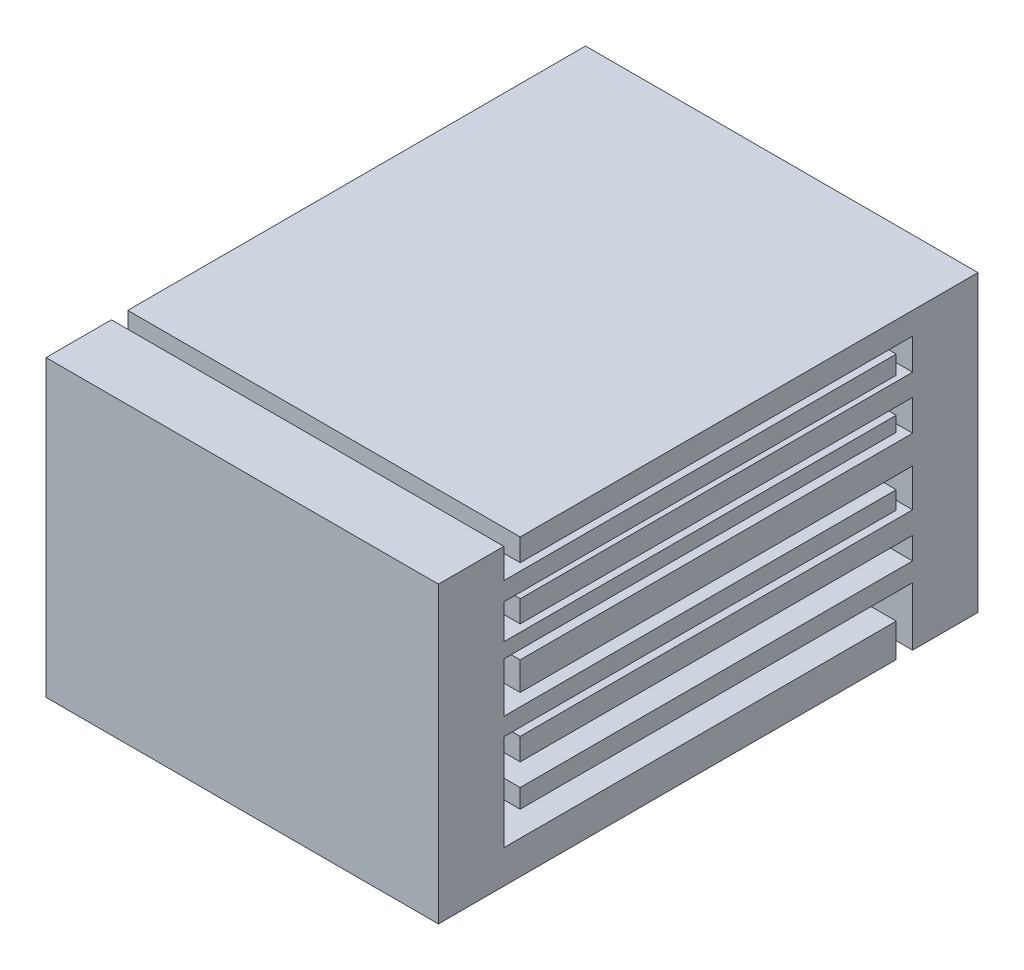
SolidWorks part; units mm, degrees
ref_plane "Front Plane" through (0, 0, 0) normal (0, 0, 1) x (1, 0, 0)
ref_plane "Top Plane" through (0, 0, 0) normal (0, 1, 0) x (1, 0, 0)
ref_plane "Right Plane" through (0, 0, 0) normal (1, 0, 0) x (0, 0, -1)
sketch "Sketch1" plane through (0, 0, 0) normal (0, 0, 1) x (1, 0, 0)
  line L1 (-60, 45) -> (60, 45)
  line L2 (-60, 45) -> (-60, -45)
  line L3 (-60, -45) -> (60, -45)
  line L4 (60, 45) -> (60, -45)
  line L5 (-60, 45) -> (60, -45) construction
  line L6 (-60, -45) -> (60, 45) construction
  point P0 (0, 0)
  dimension "D1" = 90
  dimension "D2" = 120
extrude "Boss-Extrude1" add sketch "Sketch1" along normal blind 20
sketch "Sketch2" plane through (0, 0, 20) normal (0, 0, 1) x (1, 0, 0)
  line L0 (60, -45) -> (60, 45) construction
  line L1 (-60, 45) -> (60, 45)
  line L2 (-60, 45) -> (-60, 38.1749)
  line L3 (-60, 38.1749) -> (60, 38.1749)
  line L4 (60, 45) -> (60, 38.1749)
  line L5 (-60, 45) -> (-60, -45) construction
  line L6 (-60, 28.6271) -> (60, 28.6271)
  line L7 (-60, 28.6271) -> (-60, 21.9575)
  line L8 (-60, 21.9575) -> (60, 21.9575)
  line L9 (60, 28.6271) -> (60, 21.9575)
  line L11 (-60, 12.4542) -> (60, 12.4542)
  line L12 (-60, 12.4542) -> (-60, 3.8002)
  line L13 (-60, 3.8002) -> (60, 3.8002)
  line L14 (60, 12.4542) -> (60, 3.8002)
  line L15 (-60, -7.8191) -> (60, -7.8191)
  line L16 (-60, -7.8191) -> (-60, -14.5799)
  line L17 (-60, -14.5799) -> (60, -14.5799)
  line L18 (60, -7.8191) -> (60, -14.5799)
extrude "Boss-Extrude2" add sketch "Sketch2" along normal blind 120
sketch "Sketch3" plane through (0, 0, 140) normal (0, 0, 1) x (1, 0, 0)
  line L1 (-60, 45) -> (60, 45)
  line L2 (-60, 45) -> (-60, -45)
  line L3 (-60, -45) -> (60, -45)
  line L4 (60, 45) -> (60, -45)
  dimension "D1" = 90
extrude "Boss-Extrude3" add sketch "Sketch3" along normal blind 20 from offset 5 separate body contours L2 L3 L4 L1
sketch "Sketch4" plane through (0, 0, 145) normal (0, 0, -1) x (-1, 0, 0)
  line L0 (-60, 45) -> (-60, -45) construction
  line L1 (60, -45) -> (-60, -45)
  line L2 (60, -45) -> (60, -34.7951)
  line L3 (60, -34.7951) -> (-60, -34.7951)
  line L4 (-60, -45) -> (-60, -34.7951)
  line L5 (60, 45) -> (60, -45) construction
  line L6 (60, -5.422) -> (-60, -5.422)
  line L7 (60, -5.422) -> (60, 0)
  line L8 (60, 0) -> (-60, 0)
  line L9 (-60, -5.422) -> (-60, 0)
  line L11 (60, 15.1996) -> (-60, 15.1996)
  line L12 (60, 15.1996) -> (60, 19.7321)
  line L13 (60, 19.7321) -> (-60, 19.7321)
  line L14 (-60, 15.1996) -> (-60, 19.7321)
  line L15 (60, 30.3092) -> (-60, 30.3092)
  line L16 (60, 30.3092) -> (60, 35.9257)
  line L17 (60, 35.9257) -> (-60, 35.9257)
  line L18 (-60, 30.3092) -> (-60, 35.9257)
extrude "Boss-Extrude4" add sketch "Sketch4" along normal blind 120
ref_plane "Plane1" through (-60, -14.5799, 20) normal (0, -1, 0) x (-1, 0, 0)
sketch "Sketch6" plane through (0, 0, 20) normal (0, 0, 1) x (1, 0, 0)
  line L0 (-60, -14.5799) -> (-60, -45) construction
  line L1 (-60, -21.3613) -> (60, -21.3613)
  line L2 (-60, -21.3613) -> (-60, -27.1004)
  line L3 (-60, -27.1004) -> (60, -27.1004)
  line L4 (60, -21.3613) -> (60, -27.1004)
  line L5 (60, -45) -> (60, -14.5799) construction
extrude "Boss-Extrude5" add sketch "Sketch6" along normal blind 120 contours L1 L4 L3 L2
